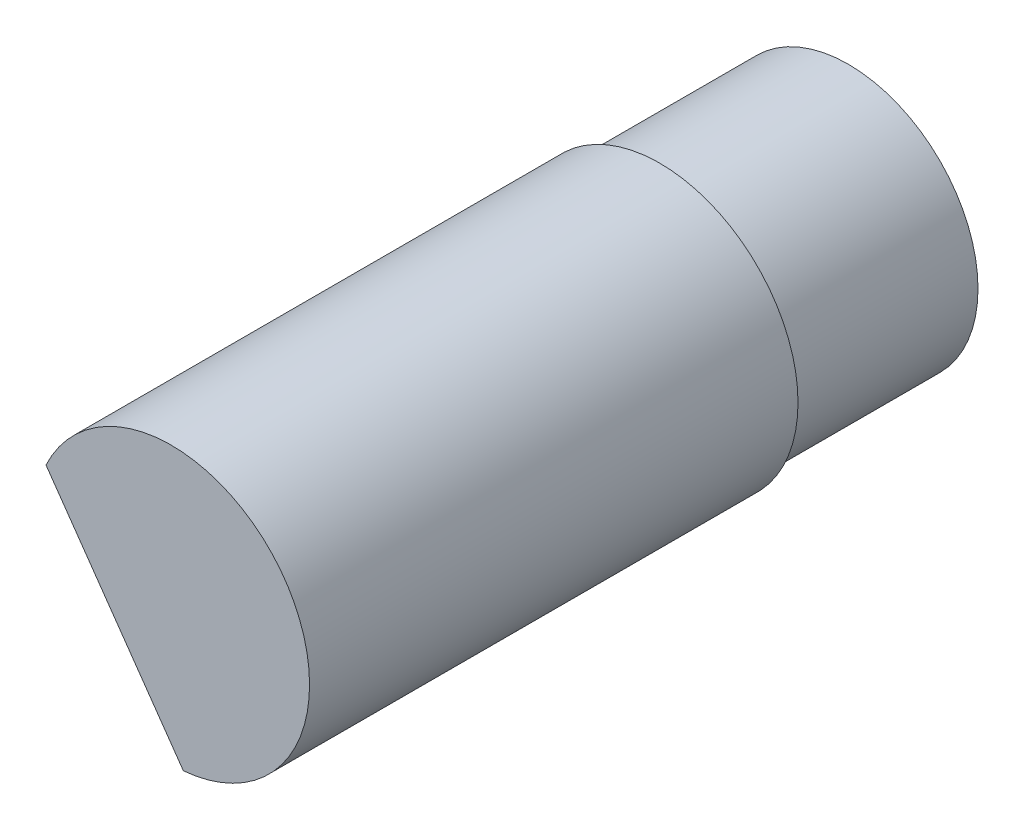
SolidWorks part; units mm, degrees
ref_plane "Front Plane" through (0, 0, 0) normal (0, 0, 1) x (1, 0, 0)
ref_plane "Top Plane" through (0, 0, 0) normal (0, 1, 0) x (1, 0, 0)
ref_plane "Right Plane" through (0, 0, 0) normal (1, 0, 0) x (0, 0, -1)
sketch "Sketch1" plane through (0, 0, 0) normal (0, 0, 1) x (1, 0, 0)
  line L0 (105.4912, 31.7818) -> (115.6611, 33.6121) construction
  circle A0 centre (110.5761, 32.6969) radius 5.9267
  dimension "D1" = 11.8533
extrude "Boss-Extrude1" add sketch "Sketch1" along normal blind 8.636
sketch "Sketch2" plane through (0, 0, 8.636) normal (0, 0, 1) x (1, 0, 0)
  circle A2 centre (110.5761, 32.6969) radius 6.3267
  circle A3 centre (110.5761, 32.6969) radius 6.3267
  dimension "D1" = 0.4
extrude "Boss-Extrude2" add sketch "Sketch2" along normal blind 18.9653
sketch "Sketch3" plane through (0, 0, 27.6013) normal (0, 0, 1) x (1, 0, 0)
  line L0 (110.5761, 32.6969) -> (105.3936, 29.0681)
  line L1 (107.9849, 30.8825) -> (111.1275, 26.3943)
  line L2 (107.9849, 30.8825) -> (104.8422, 35.3707)
  circle A1 centre (110.5761, 32.6969) radius 6.3267
  circle A2 centre (110.5761, 32.6969) radius 6.3267
  dimension "D1" = 0
extrude "Boss-Extrude3" add sketch "Sketch3" along normal blind 3.3867
